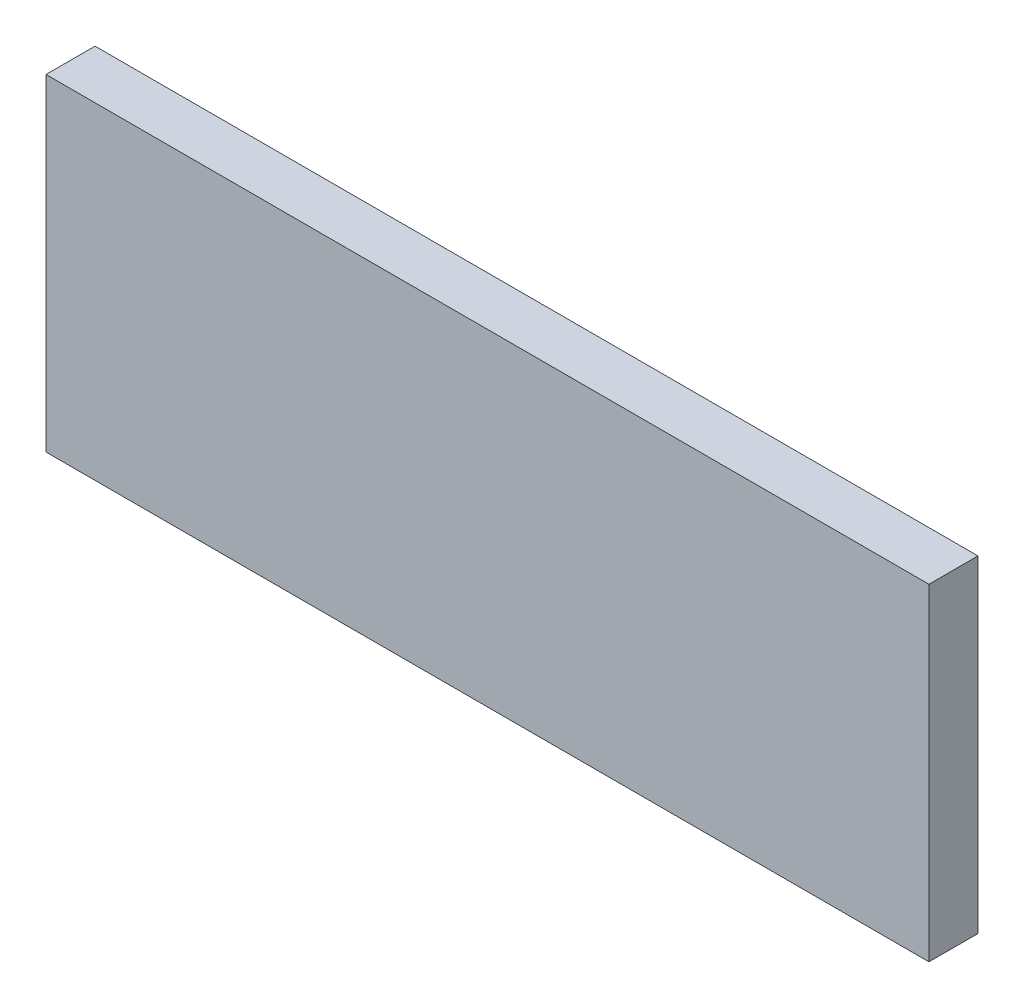
SolidWorks part; units mm, degrees
ref_plane "Front Plane" through (0, 0, 0) normal (0, 0, 1) x (1, 0, 0)
ref_plane "Top Plane" through (0, 0, 0) normal (0, 1, 0) x (1, 0, 0)
ref_plane "Right Plane" through (0, 0, 0) normal (1, 0, 0) x (0, 0, -1)
sketch "Sketch1" plane through (0, 0, 0) normal (0, 0, 1) x (1, 0, 0)
  line L0 (0, 5) -> (0, -5.1613) construction
  line L1 (-13.5, -5) -> (13.5, -5)
  line L2 (-13.5, -5) -> (-13.5, 5)
  line L3 (-13.5, 5) -> (13.5, 5)
  line L4 (13.5, -5) -> (13.5, 5)
  line L5 (-13.5, -5) -> (13.5, 5) construction
  line L6 (-13.5, 5) -> (13.5, -5) construction
  line L7 (-13.5, -1.5) -> (13.5, -1.5) construction
  circle A0 centre (-6.7, -1.5) radius 6.25 construction
  circle A1 centre (6.7, -1.5) radius 6.25 construction
  point P4 (0, 0)
  dimension "D1" = 12.5
  dimension "D2" = 6.8
  dimension "D3" = 6.5
  dimension "D4" = 27
  dimension "D5" = 10
extrude "Boss-Extrude1" add sketch "Sketch1" along normal blind 1.5
fillet "Fillet1" [suppressed] radius 2
